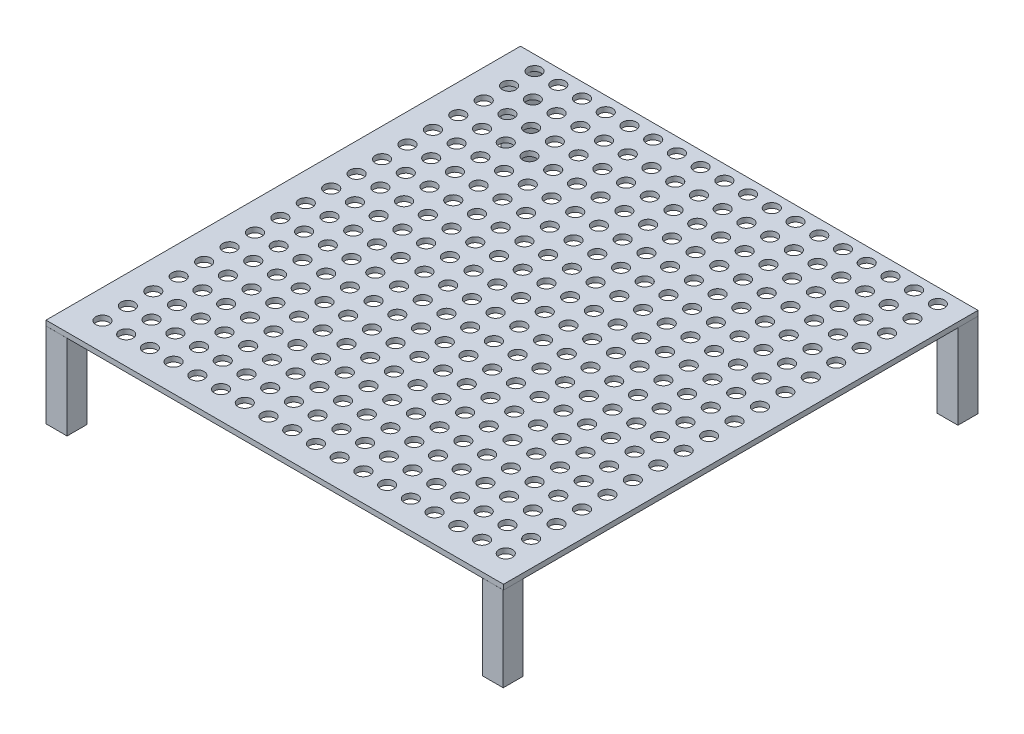
SolidWorks part; units mm, degrees
ref_plane "Front Plane" through (0, 0, 0) normal (0, 0, 1) x (1, 0, 0)
ref_plane "Top Plane" through (0, 0, 0) normal (0, 1, 0) x (1, 0, 0)
ref_plane "Right Plane" through (0, 0, 0) normal (1, 0, 0) x (0, 0, -1)
sketch "Sketch1" plane through (0, 0, 0) normal (0, 1, 0) x (1, 0, 0)
  line L0 (-133.403, 137.047) -> (136.597, 137.047)
  line L1 (-133.403, 137.047) -> (-133.403, -142.953)
  line L2 (-133.403, -142.953) -> (136.597, -142.953)
  line L3 (136.597, 137.047) -> (136.597, -142.953)
  dimension "D1" = 270
  dimension "D2" = 280
extrude "Boss-Extrude1" add sketch "Sketch1" along normal blind 3
sketch "Sketch2" plane through (0, 3, 0) normal (0, 1, 0) x (1, 0, 0)
  circle A0 centre (-116.4902, 128.4478) radius 4
  circle A1 centre (-102.4902, 128.4478) radius 4
  circle A2 centre (-88.4902, 128.4478) radius 4
  circle A3 centre (-74.4902, 128.4478) radius 4
  circle A4 centre (-60.4902, 128.4478) radius 4
  circle A5 centre (-46.4902, 128.4478) radius 4
  circle A6 centre (-32.4902, 128.4478) radius 4
  circle A7 centre (-18.4902, 128.4478) radius 4
  circle A8 centre (-4.4902, 128.4478) radius 4
  circle A9 centre (9.5098, 128.4478) radius 4
  circle A10 centre (23.5098, 128.4478) radius 4
  circle A11 centre (37.5098, 128.4478) radius 4
  circle A12 centre (51.5098, 128.4478) radius 4
  circle A13 centre (65.5098, 128.4478) radius 4
  circle A14 centre (79.5098, 128.4478) radius 4
  circle A15 centre (93.5098, 128.4478) radius 4
  circle A16 centre (107.5098, 128.4478) radius 4
  circle A17 centre (121.5098, 128.4478) radius 4
  point P3 (-116.4902, 128.4478)
  dimension "D1" = 8
  dimension "D2" = 18
extrude "Cut-Extrude1" cut sketch "Sketch2" against normal blind 132.5
pattern_linear "LPattern1" count 18 spacing 15 along (0, 0, 1) of "Cut-Extrude1"
sketch "Sketch3" plane through (0, 0, 0) normal (0, -1, 0) x (1, 0, 0)
  line L0 (1.597, 142.953) -> (1.597, -137.047) construction
  line L1 (136.4345, 142.9726) -> (124.1419, 142.9726)
  line L2 (136.4345, 142.9726) -> (136.4345, 131.2749)
  line L3 (136.4345, 131.2749) -> (124.1419, 131.2749)
  line L4 (124.1419, 142.9726) -> (124.1419, 131.2749)
  line L5 (-133.403, 142.953) -> (136.597, 142.953) construction
  line L6 (136.597, -137.047) -> (-133.403, -137.047) construction
  line L7 (-120.9479, 142.9726) -> (-120.9479, 131.2749)
  line L8 (-133.2405, 131.2749) -> (-120.9479, 131.2749)
  line L9 (-133.2405, 142.9726) -> (-133.2405, 131.2749)
  line L10 (-133.2405, 142.9726) -> (-120.9479, 142.9726)
  line L11 (-133.403, 2.953) -> (147.0872, 2.953) construction
  line L12 (-133.403, -137.047) -> (-133.403, 142.953) construction
  line L13 (124.1419, -137.0666) -> (124.1419, -125.3689)
  line L14 (136.4345, -125.3689) -> (124.1419, -125.3689)
  line L15 (136.4345, -137.0666) -> (136.4345, -125.3689)
  line L16 (136.4345, -137.0666) -> (124.1419, -137.0666)
  line L17 (-133.2405, -137.0666) -> (-120.9479, -137.0666)
  line L18 (-133.2405, -137.0666) -> (-133.2405, -125.3689)
  line L19 (-133.2405, -125.3689) -> (-120.9479, -125.3689)
  line L20 (-120.9479, -137.0666) -> (-120.9479, -125.3689)
  point P27 (141.6561, 148.2476)
extrude "Boss-Extrude2" add sketch "Sketch3" along normal blind 50
